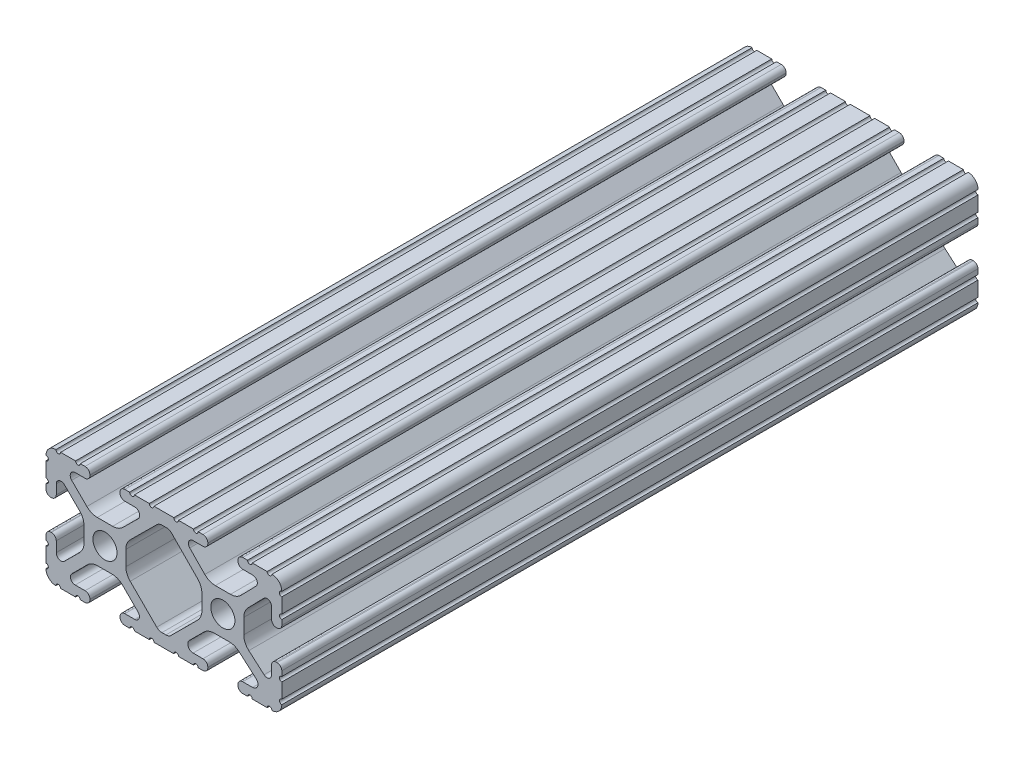
SolidWorks part; units mm, degrees
material "6105-T5 Aluminum"
ref_plane "Front Plane" through (0, 0, 0) normal (0, 0, 1) x (1, 0, 0)
ref_plane "Top Plane" through (0, 0, 0) normal (0, 1, 0) x (1, 0, 0)
ref_plane "Right Plane" through (0, 0, 0) normal (1, 0, 0) x (0, 0, -1)
sketch "Sketch1" plane through (0, 0, 0) normal (0, 0, 1) x (1, 0, 0)
  line L0 (0, 0) -> (0.0141, 4.4958) construction
  line L4 (-19.9595, -3.8694) -> (-14.2457, -9.5728)
  line L5 (-11.1543, -9.5728) -> (-5.4405, -3.8694)
  line L7 (-13.0952, 10.033) -> (-12.1485, 10.033)
  line L9 (-12.2668, -10.033) -> (-13.1332, -10.033)
  line L12 (-4.5085, -1.6223) -> (-4.5085, 1.6223)
  line L13 (-5.4171, 3.8459) -> (-11.0244, 9.5611)
  line L14 (-14.204, 9.5765) -> (-19.952, 3.8768)
  line L15 (-20.8915, 1.6223) -> (-20.8915, -1.6223)
  line L16 (9.5504, 12.7) -> (6.3331, 12.7)
  line L17 (5.3171, 12.7) -> (4.2875, 12.7)
  line L18 (3.2385, 11.651) -> (3.2385, 11.5392)
  line L19 (4.2875, 10.4902) -> (6.4164, 10.4902)
  line L20 (7.1441, 8.7652) -> (3.919, 5.4551)
  line L21 (1.6449, 4.4958) -> (-1.6167, 4.4958)
  line L22 (-3.883, 5.4472) -> (-7.1358, 8.7627)
  line L23 (-6.4106, 10.4902) -> (-4.2875, 10.4902)
  line L24 (-3.2385, 11.5392) -> (-3.2385, 11.651)
  line L25 (-4.2875, 12.7) -> (-5.3171, 12.7)
  line L26 (-6.3331, 12.7) -> (-9.5504, 12.7)
  line L27 (-10.5664, 12.7) -> (-14.8336, 12.7)
  line L28 (-15.8496, 12.7) -> (-19.0669, 12.7)
  line L29 (-20.0829, 12.7) -> (-21.1125, 12.7)
  line L30 (-22.1615, 11.651) -> (-22.1615, 11.5392)
  line L31 (-21.1125, 10.4902) -> (-18.9836, 10.4902)
  line L32 (-18.2326, 8.6661) -> (-21.51, 5.4163)
  line L33 (-23.7455, 4.4958) -> (-27.0545, 4.4958)
  line L34 (-29.29, 5.4163) -> (-32.5674, 8.6661)
  line L35 (-31.8164, 10.4902) -> (-29.6875, 10.4902)
  line L36 (-28.6385, 11.5392) -> (-28.6385, 11.651)
  line L37 (-29.6875, 12.7) -> (-30.7171, 12.7)
  line L38 (-31.7331, 12.7) -> (-34.9504, 12.7)
  line L39 (-38.1, 9.5504) -> (-38.1, 6.3331)
  line L40 (-38.1, 5.3171) -> (-38.1, 4.2375)
  line L41 (-37.101, 3.2385) -> (-36.9392, 3.2385)
  line L42 (-35.8902, 4.2875) -> (-35.8902, 6.3347)
  line L43 (-34.134, 7.0665) -> (-30.848, 3.8082)
  line L44 (-29.9085, 1.5536) -> (-29.9085, -1.6952)
  line L45 (-30.8405, -3.9423) -> (-34.1316, -7.2274)
  line L46 (-35.8902, -6.498) -> (-35.8902, -4.2875)
  line L47 (-36.9392, -3.2385) -> (-37.051, -3.2385)
  line L48 (-38.1, -4.2875) -> (-38.1, -5.3171)
  line L49 (-38.1, -6.3331) -> (-38.1, -9.5504)
  line L50 (-34.9504, -12.7) -> (-31.7331, -12.7)
  line L51 (-30.7171, -12.7) -> (-29.6875, -12.7)
  line L52 (-28.6384, -11.651) -> (-28.6384, -11.5392)
  line L53 (-29.6875, -10.4902) -> (-31.8164, -10.4902)
  line L54 (-32.5341, -8.7551) -> (-29.1966, -5.4237)
  line L55 (-26.9536, -4.4958) -> (-23.8464, -4.4958)
  line L56 (-21.6034, -5.4237) -> (-18.2659, -8.7551)
  line L57 (-18.9836, -10.4902) -> (-21.1125, -10.4902)
  line L58 (-22.1616, -11.5392) -> (-22.1616, -11.651)
  line L59 (-21.1125, -12.7) -> (-20.0829, -12.7)
  line L60 (-19.0669, -12.7) -> (-15.8496, -12.7)
  line L61 (-14.8336, -12.7) -> (-10.5664, -12.7)
  line L62 (-9.5504, -12.7) -> (-6.3331, -12.7)
  line L63 (-5.3171, -12.7) -> (-4.2875, -12.7)
  line L64 (-3.2384, -11.651) -> (-3.2384, -11.5392)
  line L65 (-4.2875, -10.4902) -> (-6.4106, -10.4902)
  line L66 (-7.2193, -8.5353) -> (-4.1021, -5.4237)
  line L67 (-1.8591, -4.4958) -> (1.4026, -4.4958)
  line L68 (3.4879, -5.2766) -> (7.1682, -8.4822)
  line L69 (6.4164, -10.4902) -> (4.2875, -10.4902)
  line L70 (3.2384, -11.5392) -> (3.2384, -11.651)
  line L71 (4.2875, -12.7) -> (5.3171, -12.7)
  line L72 (6.3331, -12.7) -> (9.5504, -12.7)
  line L73 (12.7, -9.5504) -> (12.7, -6.3331)
  line L74 (12.7, -5.3171) -> (12.7, -4.2375)
  line L75 (11.701, -3.2385) -> (11.4892, -3.2385)
  line L76 (10.4902, -4.2375) -> (10.4902, -6.1559)
  line L77 (8.884, -6.8869) -> (5.5982, -4.025)
  line L78 (4.5085, -1.6308) -> (4.5085, 1.6308)
  line L79 (5.4094, 3.8465) -> (8.8263, 7.3534)
  line L80 (10.4902, 6.6769) -> (10.4902, 4.2375)
  line L81 (11.4892, 3.2385) -> (11.701, 3.2385)
  line L82 (12.7, 4.2375) -> (12.7, 5.3171)
  line L83 (12.7, 6.3332) -> (12.7, 9.5504)
  circle A0 centre (-25.4, 0) radius 2.6035
  circle A1 centre (0, 0) radius 2.6035
  arc A2 (-13.0952, 10.033) -> (-14.204, 9.5765) centre (-13.0952, 8.4582) ccw
  arc A3 (-12.1485, 10.033) -> (-11.0244, 9.5611) centre (-12.1485, 8.4582) cw
  arc A4 (-20.8915, -1.6223) -> (-19.9595, -3.8694) centre (-17.7165, -1.6223) ccw
  arc A5 (-13.1332, -10.033) -> (-14.2457, -9.5728) centre (-13.1332, -8.4582) cw
  arc A6 (-5.4405, -3.8694) -> (-4.5085, -1.6223) centre (-7.6835, -1.6223) ccw
  arc A7 (-4.5085, 1.6223) -> (-5.4171, 3.8459) centre (-7.6835, 1.6223) ccw
  arc A8 (-12.2668, -10.033) -> (-11.1543, -9.5728) centre (-12.2668, -8.4582) ccw
  arc A9 (-19.952, 3.8768) -> (-20.8915, 1.6223) centre (-17.7165, 1.6223) ccw
  arc A16 (12.6998, 10.5664) -> (10.5664, 12.6998) centre (10.5918, 10.5918) ccw
  arc A17 (9.5504, 12.7) -> (10.5664, 12.6998) centre (10.0584, 12.7) ccw
  arc A18 (5.3171, 12.7) -> (6.3331, 12.7) centre (5.8251, 12.7) ccw
  arc A19 (4.2875, 12.7) -> (3.2385, 11.651) centre (4.2875, 11.651) ccw
  arc A20 (3.2385, 11.5392) -> (4.2875, 10.4902) centre (4.2875, 11.5392) ccw
  arc A21 (7.1441, 8.7652) -> (6.4164, 10.4902) centre (6.4164, 9.4742) ccw
  arc A22 (1.6449, 4.4958) -> (3.919, 5.4551) centre (1.6449, 7.6708) ccw
  arc A23 (-3.883, 5.4472) -> (-1.6167, 4.4958) centre (-1.6167, 7.6708) ccw
  arc A24 (-6.4106, 10.4902) -> (-7.1358, 8.7627) centre (-6.4106, 9.4742) ccw
  arc A25 (-4.2875, 10.4902) -> (-3.2385, 11.5392) centre (-4.2875, 11.5392) ccw
  arc A26 (-3.2385, 11.651) -> (-4.2875, 12.7) centre (-4.2875, 11.651) ccw
  arc A27 (-6.3331, 12.7) -> (-5.3171, 12.7) centre (-5.8251, 12.7) ccw
  arc A28 (-10.5664, 12.7) -> (-9.5504, 12.7) centre (-10.0584, 12.7) ccw
  arc A29 (-15.8496, 12.7) -> (-14.8336, 12.7) centre (-15.3416, 12.7) ccw
  arc A30 (-20.0829, 12.7) -> (-19.0669, 12.7) centre (-19.5749, 12.7) ccw
  arc A31 (-21.1125, 12.7) -> (-22.1615, 11.651) centre (-21.1125, 11.651) ccw
  arc A32 (-22.1615, 11.5392) -> (-21.1125, 10.4902) centre (-21.1125, 11.5392) ccw
  arc A33 (-18.2326, 8.6661) -> (-18.9836, 10.4902) centre (-18.9836, 9.4235) ccw
  arc A34 (-23.7455, 4.4958) -> (-21.51, 5.4163) centre (-23.7455, 7.6708) ccw
  arc A35 (-29.29, 5.4163) -> (-27.0545, 4.4958) centre (-27.0545, 7.6708) ccw
  arc A36 (-31.8164, 10.4902) -> (-32.5674, 8.6661) centre (-31.8164, 9.4235) ccw
  arc A37 (-29.6875, 10.4902) -> (-28.6385, 11.5392) centre (-29.6875, 11.5392) ccw
  arc A38 (-28.6385, 11.651) -> (-29.6875, 12.7) centre (-29.6875, 11.651) ccw
  arc A39 (-31.7331, 12.7) -> (-30.7171, 12.7) centre (-31.2251, 12.7) ccw
  arc A40 (-35.9664, 12.6998) -> (-34.9504, 12.7) centre (-35.4584, 12.7) ccw
  arc A41 (-35.9664, 12.6998) -> (-38.0998, 10.5664) centre (-35.9918, 10.5918) ccw
  arc A42 (-38.1, 9.5504) -> (-38.0998, 10.5664) centre (-38.1, 10.0584) ccw
  arc A43 (-38.1, 5.3171) -> (-38.1, 6.3331) centre (-38.1, 5.8251) ccw
  arc A44 (-38.1, 4.2375) -> (-37.101, 3.2385) centre (-37.101, 4.2375) ccw
  arc A45 (-36.9392, 3.2385) -> (-35.8902, 4.2875) centre (-36.9392, 4.2875) ccw
  arc A46 (-34.134, 7.0665) -> (-35.8902, 6.3347) centre (-34.8596, 6.3347) ccw
  arc A47 (-29.9085, 1.5536) -> (-30.848, 3.8082) centre (-33.0835, 1.5536) ccw
  arc A48 (-30.8405, -3.9423) -> (-29.9085, -1.6952) centre (-33.0835, -1.6952) ccw
  arc A49 (-35.8902, -6.498) -> (-34.1316, -7.2274) centre (-34.8596, -6.498) ccw
  arc A50 (-35.8902, -4.2875) -> (-36.9392, -3.2385) centre (-36.9392, -4.2875) ccw
  arc A51 (-37.051, -3.2385) -> (-38.1, -4.2875) centre (-37.051, -4.2875) ccw
  arc A52 (-38.1, -6.3331) -> (-38.1, -5.3171) centre (-38.1, -5.8251) ccw
  arc A53 (-38.0998, -10.5664) -> (-38.1, -9.5504) centre (-38.1, -10.0584) ccw
  arc A54 (-38.0998, -10.5664) -> (-35.9664, -12.6998) centre (-35.9918, -10.5918) ccw
  arc A55 (-34.9504, -12.7) -> (-35.9664, -12.6998) centre (-35.4584, -12.7) ccw
  arc A56 (-30.7171, -12.7) -> (-31.7331, -12.7) centre (-31.2251, -12.7) ccw
  arc A57 (-29.6875, -12.7) -> (-28.6384, -11.651) centre (-29.6875, -11.651) ccw
  arc A58 (-28.6384, -11.5392) -> (-29.6875, -10.4902) centre (-29.6875, -11.5392) ccw
  arc A59 (-32.5341, -8.7551) -> (-31.8164, -10.4902) centre (-31.8164, -9.4742) ccw
  arc A60 (-26.9536, -4.4958) -> (-29.1966, -5.4237) centre (-26.9536, -7.6708) ccw
  arc A61 (-21.6034, -5.4237) -> (-23.8464, -4.4958) centre (-23.8464, -7.6708) ccw
  arc A62 (-18.9836, -10.4902) -> (-18.2659, -8.7551) centre (-18.9836, -9.4742) ccw
  arc A63 (-21.1125, -10.4902) -> (-22.1616, -11.5392) centre (-21.1125, -11.5392) ccw
  arc A64 (-22.1616, -11.651) -> (-21.1125, -12.7) centre (-21.1125, -11.651) ccw
  arc A65 (-19.0669, -12.7) -> (-20.0829, -12.7) centre (-19.5749, -12.7) ccw
  arc A66 (-14.8336, -12.7) -> (-15.8496, -12.7) centre (-15.3416, -12.7) ccw
  arc A67 (-9.5504, -12.7) -> (-10.5664, -12.7) centre (-10.0584, -12.7) ccw
  arc A68 (-5.3171, -12.7) -> (-6.3331, -12.7) centre (-5.8251, -12.7) ccw
  arc A69 (-4.2875, -12.7) -> (-3.2384, -11.651) centre (-4.2875, -11.651) ccw
  arc A70 (-3.2384, -11.5392) -> (-4.2875, -10.4902) centre (-4.2875, -11.5392) ccw
  arc A71 (-7.2193, -8.5353) -> (-6.4106, -10.4902) centre (-6.4106, -9.3455) ccw
  arc A72 (-1.8591, -4.4958) -> (-4.1021, -5.4237) centre (-1.8591, -7.6708) ccw
  arc A73 (3.4879, -5.2766) -> (1.4026, -4.4958) centre (1.4026, -7.6708) ccw
  arc A74 (6.4164, -10.4902) -> (7.1682, -8.4822) centre (6.4164, -9.3455) ccw
  arc A75 (4.2875, -10.4902) -> (3.2384, -11.5392) centre (4.2875, -11.5392) ccw
  arc A76 (3.2384, -11.651) -> (4.2875, -12.7) centre (4.2875, -11.651) ccw
  arc A77 (6.3331, -12.7) -> (5.3171, -12.7) centre (5.8251, -12.7) ccw
  arc A78 (10.5664, -12.6998) -> (9.5504, -12.7) centre (10.0584, -12.7) ccw
  arc A79 (10.5664, -12.6998) -> (12.6998, -10.5664) centre (10.5918, -10.5918) ccw
  arc A80 (12.7, -9.5504) -> (12.6998, -10.5664) centre (12.7, -10.0584) ccw
  arc A81 (12.7, -5.3171) -> (12.7, -6.3331) centre (12.7, -5.8251) ccw
  arc A82 (12.7, -4.2375) -> (11.701, -3.2385) centre (11.701, -4.2375) ccw
  arc A83 (11.4892, -3.2385) -> (10.4902, -4.2375) centre (11.4892, -4.2375) ccw
  arc A84 (8.884, -6.8869) -> (10.4902, -6.1559) centre (9.5207, -6.1559) ccw
  arc A85 (4.5085, -1.6308) -> (5.5982, -4.025) centre (7.6835, -1.6308) ccw
  arc A86 (5.4094, 3.8465) -> (4.5085, 1.6308) centre (7.6835, 1.6308) ccw
  arc A87 (10.4902, 6.6769) -> (8.8263, 7.3534) centre (9.5207, 6.6769) ccw
  arc A88 (10.4902, 4.2375) -> (11.4892, 3.2385) centre (11.4892, 4.2375) ccw
  arc A89 (11.701, 3.2385) -> (12.7, 4.2375) centre (11.701, 4.2375) ccw
  arc A90 (12.7, 6.3332) -> (12.7, 5.3171) centre (12.7, 5.8251) ccw
  arc A91 (12.6998, 10.5664) -> (12.7, 9.5504) centre (12.7, 10.0584) ccw
  dimension "D1" = 5.207
  dimension "D6" = 6.477
  dimension "D7" = 14.859
  dimension "D14" = 1.5748
  dimension "D16" = 1.5748
  dimension "D15" = 3.175
  dimension "D3" = 50.8
  dimension "D4" = 25.4
  dimension "D5" = 8.2042
  dimension "D8" = 2.2098
  dimension "D9" = 2.2098
  dimension "D10" = 2.2098
  dimension "D11" = 2.2098
  dimension "D12" = 2.2098
  dimension "D13" = 6.477
extrude "Extrude1" add sketch "Sketch1" against normal blind 150
